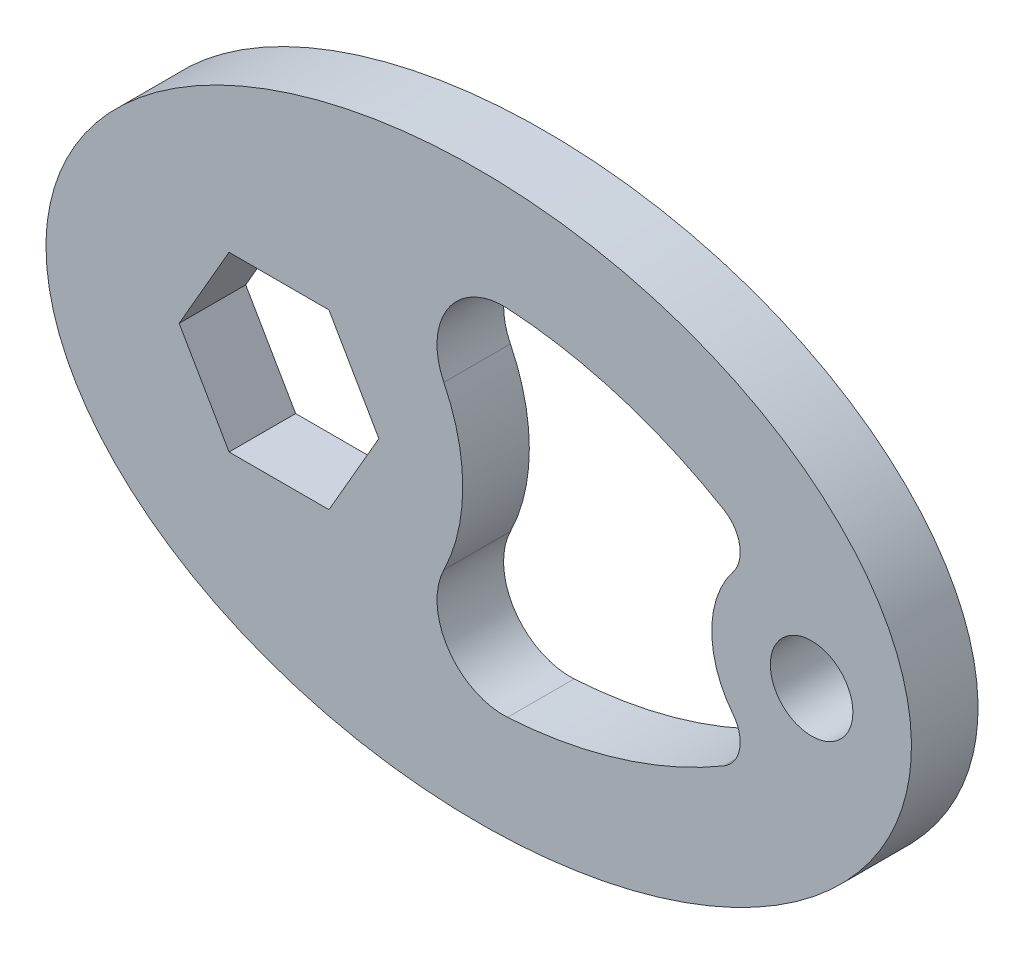
SolidWorks part; units mm, degrees
ref_plane "Front Plane" through (0, 0, 0) normal (0, 0, 1) x (1, 0, 0)
ref_plane "Top Plane" through (0, 0, 0) normal (0, 1, 0) x (1, 0, 0)
ref_plane "Right Plane" through (0, 0, 0) normal (1, 0, 0) x (0, 0, -1)
sketch "Sketch1" plane through (0, 0, 0) normal (0, 0, 1) x (1, 0, 0)
  line L0 (-3.25, 0) -> (3.25, 0) construction
  line L1 (-0.75, 0) -> (-1.125, 0.6495)
  line L2 (-1.125, 0.6495) -> (-1.875, 0.6495)
  line L3 (-1.875, 0.6495) -> (-2.25, 0)
  line L4 (-2.25, 0) -> (-1.875, -0.6495)
  line L5 (-1.875, -0.6495) -> (-1.125, -0.6495)
  line L6 (-1.125, -0.6495) -> (-0.75, 0)
  circle A0 centre (2.5, 0) radius 0.31
  arc A1 (1.9103, 0.4634) -> (1.9103, -0.4634) centre (2.5, 0) ccw
  arc A2 (-0.262, -0.6097) -> (-0.262, 0.6097) centre (-1.5, 0) ccw
  arc A4 (1.8409, 0.8332) -> (0.2165, 1.3297) centre (0, -2.2838) ccw
  arc A5 (-0.262, 0.6097) -> (0.2165, 1.3297) centre (0.1866, 0.8306) cw
  arc A6 (1.9103, 0.4634) -> (1.8409, 0.8332) centre (1.7137, 0.6179) ccw
  arc A7 (1.9103, -0.4634) -> (1.8409, -0.8332) centre (1.7137, -0.6179) cw
  arc A8 (1.8409, -0.8332) -> (0.2165, -1.3297) centre (0, 2.2838) cw
  arc A9 (-0.262, -0.6097) -> (0.2165, -1.3297) centre (0.1866, -0.8306) ccw
  circle A10 centre (-1.5, 0) radius 0.75 construction
  ellipse E0 centre (0, 0) end of major axis (-3.25, 0) minor radius 2.125
  point P31 (0, 0)
  dimension "D3" = 0.75
  dimension "D4" = 0.75
  dimension "D5" = 1.5
  dimension "D6" = 0.5
  dimension "D7" = 3.62
  dimension "D8" = 1.5
  dimension "D9" = 0.5
  dimension "D10" = 1.38
  dimension "D11" = 3.62
  dimension "D12" = 0.25
  dimension "D13" = 0.62
  dimension "D14" = 3.62
  dimension "D15" = 0.25
  dimension "D16" = 0.75
  dimension "D1" = 6.5
  dimension "D2" = 4.25
extrude "Boss-Extrude1" add sketch "Sketch1" along normal blind 0.5
